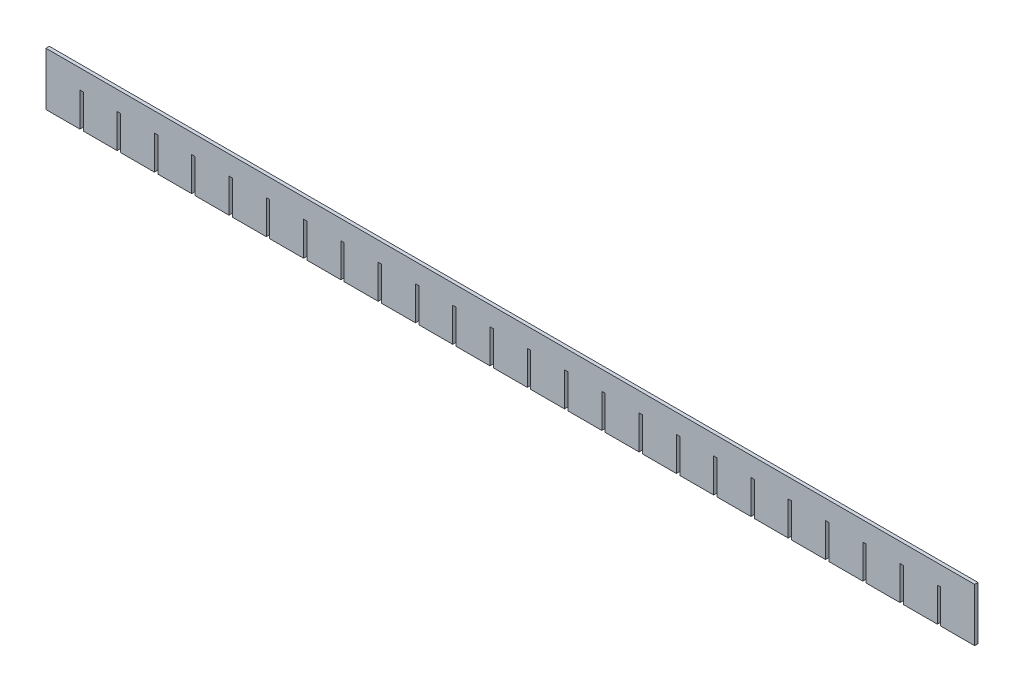
SolidWorks part; units mm, degrees
ref_plane "Ebene vorne" through (0, 0, 0) normal (0, 0, 1) x (1, 0, 0)
ref_plane "Ebene oben" through (0, 0, 0) normal (0, 1, 0) x (1, 0, 0)
ref_plane "Ebene rechts" through (0, 0, 0) normal (1, 0, 0) x (0, 0, -1)
sketch "Sketch1" plane through (0, 0, 0) normal (0, 0, 1) x (1, 0, 0)
  line L1 (-411, -23.5) -> (411, -23.5)
  line L2 (-411, -23.5) -> (-411, 23.5)
  line L3 (-411, 23.5) -> (411, 23.5)
  line L4 (411, -23.5) -> (411, 23.5)
  line L5 (-411, -23.5) -> (411, 23.5) construction
  line L6 (-411, 23.5) -> (411, -23.5) construction
  point P0 (0, 0)
  dimension "D1" = 47
  dimension "D2" = 822
extrude "Boss-Extrude1" add sketch "Sketch1" along normal blind 3
sketch "Sketch2" plane through (0, 0, 3) normal (0, 0, 1) x (1, 0, 0)
  line L6 (-411, -23.5) -> (-381, -23.5)
  line L7 (-411, -23.5) -> (411, -23.5) construction
  line L8 (-381, -23.5) -> (-381, 6.5)
  line L9 (-381, 6.5) -> (-378, 6.5)
  line L10 (-378, 6.5) -> (-378, -23.5)
  line L11 (-381, -23.5) -> (-378, -23.5)
  dimension "D1" = 30
  dimension "D2" = 30
  dimension "D3" = 3
extrude "Cut-Extrude1" cut sketch "Sketch2" against normal through all contours L11 L10 L9 L8
pattern_linear "LPattern1" count 24 spacing 33 along (1, 0, 0) of "Cut-Extrude1"
